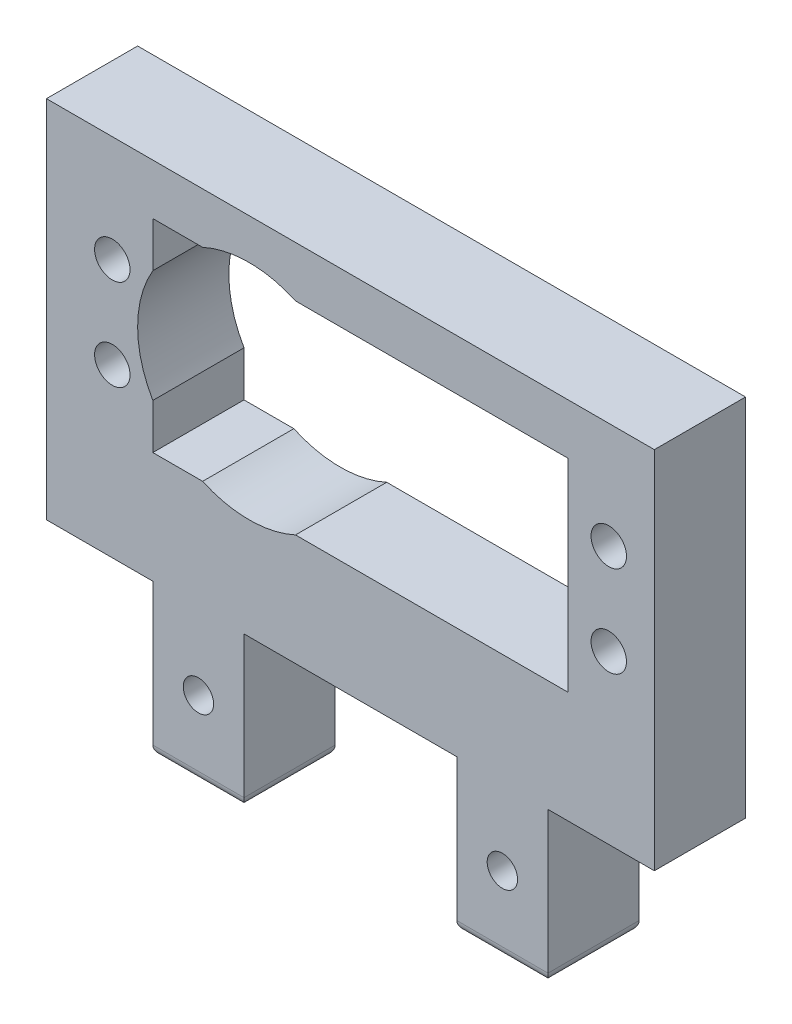
SolidWorks part; units mm, degrees
ref_plane "Alzado" through (0, 0, 0) normal (0, 0, 1) x (1, 0, 0)
ref_plane "Planta" through (0, 0, 0) normal (0, 1, 0) x (1, 0, 0)
ref_plane "Vista lateral" through (0, 0, 0) normal (1, 0, 0) x (0, 0, -1)
sketch "Croquis1" plane through (0, 0, 0) normal (0, 0, 1) x (1, 0, 0)
  line L0 (10.5, -15) -> (49.5, -15) construction
  line L1 (0, 0) -> (60, 0)
  line L2 (0, 0) -> (0, 36)
  line L3 (0, 36) -> (60, 36)
  line L4 (60, 0) -> (60, 36)
  line L5 (10.5, -7.5) -> (49.5, -7.5) construction
  line L6 (10.5, -15) -> (19.5, -15)
  line L7 (10.5, -15) -> (10.5, 0)
  line L8 (10.5, 0) -> (19.5, 0)
  line L9 (19.5, -15) -> (19.5, 0)
  line L10 (49.5, -15) -> (40.5, -15)
  line L11 (49.5, -15) -> (49.5, 0)
  line L12 (49.5, 0) -> (40.5, 0)
  line L13 (40.5, -15) -> (40.5, 0)
  line L14 (10.5, 31) -> (51.5, 31)
  line L15 (10.5, 31) -> (10.5, 11)
  line L16 (10.5, 11) -> (51.5, 11)
  line L17 (51.5, 31) -> (51.5, 11)
  line L18 (15, -15) -> (15, 0) construction
  line L19 (45, -15) -> (45, 0) construction
  line L20 (55.5, 35.4132) -> (55.5, -2.9176) construction
  line L21 (6.5, 40.3733) -> (6.5, 2.0424) construction
  line L22 (6.5, 21) -> (55.5, 21) construction
  line L23 (6.5, 25.5) -> (55.5, 25.5) construction
  line L24 (6.5, 16.5) -> (55.5, 16.5) construction
  circle A0 centre (6.5, 25.5) radius 1.75
  circle A1 centre (6.5, 16.5) radius 1.75
  circle A2 centre (55.5, 25.5) radius 1.75
  circle A3 centre (55.5, 16.5) radius 1.75
  circle A4 centre (15, -7.5) radius 1.5
  circle A5 centre (45, -7.5) radius 1.5
  circle A6 centre (20, 21) radius 11
  point P37 (20, 21)
  dimension "D14" = 3.5
  dimension "D15" = 3.5
  dimension "D16" = 3.5
  dimension "D17" = 3.5
  dimension "D21" = 3
  dimension "D22" = 3
  dimension "D23" = 22
  dimension "D1" = 15
  dimension "D2" = 10.5
  dimension "D3" = 9
  dimension "D4" = 10.5
  dimension "D5" = 9
  dimension "D6" = 60
  dimension "D7" = 41
  dimension "D8" = 4
  dimension "D9" = 4
  dimension "D10" = 20
  dimension "D11" = 10
  dimension "D12" = 4.5
  dimension "D13" = 4.5
  dimension "D18" = 9.5
  dimension "D19" = 21
  dimension "D20" = 5
  dimension "D24" = 20
extrude "Saliente-Extruir1" add sketch "Croquis1" along normal blind 9 contours L1 L4 L3 L2 A6 L14 L17 L16 L15 A3 A2 A1 A0 | L6 L9 L1 L7 A4 | L13 L10 L11 L1 A5
fillet "Redondeo1" radius 1 8 edges at (40.5, -15, 4.5) (45, -15, 9) (49.5, -15, 4.5) (45, -15, 0) (10.5, -15, 4.5) (15, -15, 9) (19.5, -15, 4.5) (15, -15, 0)
